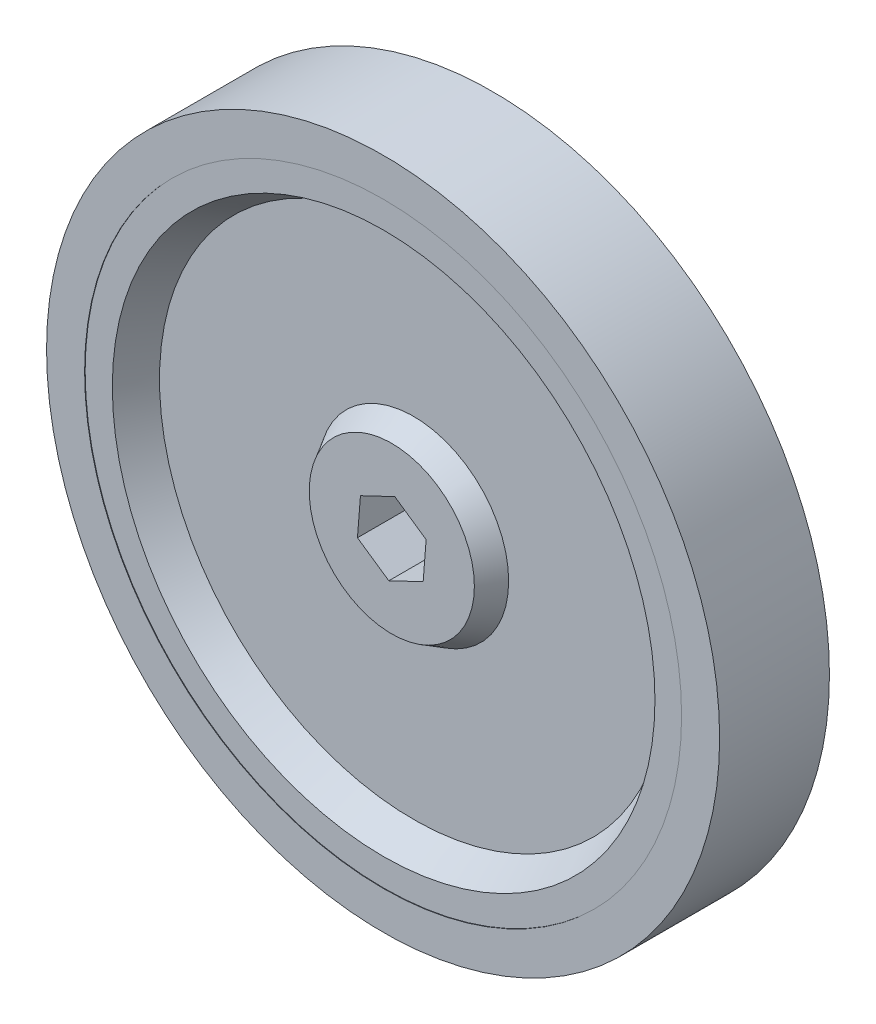
SolidWorks part; units mm, degrees
ref_plane "Front Plane" through (0, 0, 0) normal (0, 0, 1) x (1, 0, 0)
ref_plane "Top Plane" through (0, 0, 0) normal (0, 1, 0) x (1, 0, 0)
ref_plane "Right Plane" through (0, 0, 0) normal (1, 0, 0) x (0, 0, -1)
sketch "Sketch1" plane through (0, 0, 0) normal (0, 0, 1) x (1, 0, 0)
  circle A0 centre (0, 0) radius 61.9125
extrude "Boss-Extrude1" add sketch "Sketch1" along normal mid plane 20
sketch "Sketch4" plane through (0, 0, 10) normal (0, 0, 1) x (1, 0, 0)
  circle A0 centre (0, 0) radius 49.9125
extrude "Cut-Extrude1" cut sketch "Sketch4" against normal blind 5.5 draft 30
sketch "Sketch5" plane through (0, 0, -10) normal (0, 0, -1) x (-1, 0, 0)
  circle A0 centre (0, 0) radius 49.9125
extrude "Cut-Extrude2" cut sketch "Sketch5" against normal blind 5.5 draft 30
sketch "Sketch6" plane through (0, 0, 4.5) normal (0, 0, 1) x (1, 0, 0)
  circle A0 centre (0, 0) radius 17.5
extrude "Boss-Extrude2" add sketch "Sketch6" along normal blind 4 draft 30 contours A0
sketch "Sketch9" plane through (0, 0, -4.5) normal (0, 0, -1) x (-1, 0, 0)
  circle A0 centre (0, 0) radius 17.5
extrude "Boss-Extrude3" add sketch "Sketch9" along normal blind 4 draft 30
sketch "Sketch10" plane through (0, 0, -8.5) normal (0, 0, -1) x (-1, 0, 0)
  line L1 (6.3179, -3.014) -> (5.7692, 3.9644)
  line L2 (5.7692, 3.9644) -> (-0.5487, 6.9785)
  line L3 (-0.5487, 6.9785) -> (-6.3179, 3.014)
  line L4 (-6.3179, 3.014) -> (-5.7692, -3.9644)
  line L5 (-5.7692, -3.9644) -> (0.5487, -6.9785)
  line L6 (0.5487, -6.9785) -> (6.3179, -3.014)
  circle A0 centre (0, 0) radius 6.0622 construction
  dimension "D1" = 7
extrude "Cut-Extrude4" cut sketch "Sketch10" against normal blind 24
sketch "Sketch12" plane through (0, 0, 10) normal (0, 0, 1) x (1, 0, 0)
  circle A0 centre (0, 0) radius 54.9125
  circle A2 centre (0, 0) radius 49.9125
  circle A3 centre (0, 0) radius 61.9125
  dimension "D1" = 5
extrude "Boss-Extrude4" add sketch "Sketch12" along normal blind 0.1 contours A3 | A0
sketch "Sketch14" plane through (0, 0, -10) normal (0, 0, -1) x (-1, 0, 0)
  circle A0 centre (0, 0) radius 49.9125
  circle A1 centre (0, 0) radius 54.9125
  circle A2 centre (0, 0) radius 61.9125
  dimension "D1" = 5
extrude "Boss-Extrude5" add sketch "Sketch14" along normal blind 0.1 contours A2 | A1
